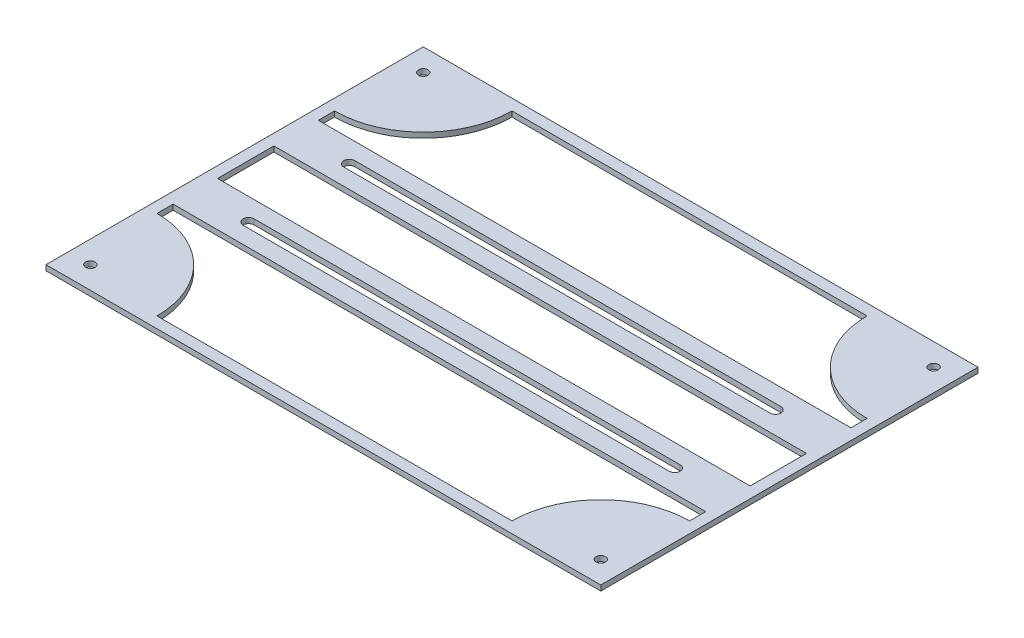
SolidWorks part; units mm, degrees
material "Acrylic (Medium-high impact)"
ref_plane "Front Plane" through (0, 0, 0) normal (0, 0, 1) x (1, 0, 0)
ref_plane "Top Plane" through (0, 0, 0) normal (0, 1, 0) x (1, 0, 0)
ref_plane "Right Plane" through (0, 0, 0) normal (1, 0, 0) x (0, 0, -1)
sketch "Sketch1" plane through (0, 0, 0) normal (0, 1, 0) x (1, 0, 0)
  line L0 (-76.2, -25.4) -> (-76.2, -20.7675)
  line L1 (79.375, -53.975) -> (-79.375, -53.975)
  line L2 (79.375, -53.975) -> (79.375, 53.975)
  line L3 (79.375, 53.975) -> (-79.375, 53.975)
  line L4 (-79.375, -53.975) -> (-79.375, 53.975)
  line L5 (79.375, -53.975) -> (-79.375, 53.975) construction
  line L6 (79.375, 53.975) -> (-79.375, -53.975) construction
  line L7 (50.8, -50.8) -> (-50.8, -50.8)
  line L8 (76.2, -25.4) -> (76.2, -20.7675)
  line L10 (76.2, -20.7675) -> (-76.2, -20.7675)
  line L11 (76.2, -8.0675) -> (-76.2, -8.0675)
  line L12 (0, 0) -> (-76.2, 0) construction
  line L13 (76.2, 8.0675) -> (-76.2, 8.0675)
  line L14 (76.2, 20.7675) -> (-76.2, 20.7675)
  line L15 (-76.2, -8.0675) -> (-76.2, 8.0675)
  line L16 (-76.2, -50.8) -> (-76.2, 50.8) construction
  line L17 (76.2, -8.0675) -> (76.2, 8.0675)
  line L18 (76.2, -50.8) -> (76.2, 50.8) construction
  line L19 (-76.2, 20.7675) -> (-76.2, 25.4)
  line L20 (76.2, 20.7675) -> (76.2, 25.4)
  line L21 (0, 0) -> (0, 34.6317) construction
  line L22 (76.2, 50.8) -> (-76.2, 50.8) construction
  line L23 (76.2, -50.8) -> (-76.2, -50.8) construction
  line L24 (50.8, 50.8) -> (-50.8, 50.8)
  arc A0 (-50.8, -50.8) -> (-76.2, -25.4) centre (-76.2, -50.8) ccw
  arc A1 (50.8, -50.8) -> (76.2, -25.4) centre (76.2, -50.8) cw
  arc A2 (50.8, 50.8) -> (76.2, 25.4) centre (76.2, 50.8) ccw
  arc A3 (-50.8, 50.8) -> (-76.2, 25.4) centre (-76.2, 50.8) cw
  point P0 (0, 0)
  dimension "D6" = 3.175
  dimension "D4" = 25.4
  dimension "D1" = 107.95
  dimension "D2" = 158.75
  dimension "D5" = 12.7
  dimension "D3" = 3.175
extrude "Boss-Extrude1" add sketch "Sketch1" along normal blind 1.524
sketch "Sketch3" plane through (0, 1.524, 0) normal (0, 1, 0) x (1, 0, 0)
  line L0 (-60.96, 14.4175) -> (60.96, 14.4175) construction
  line L1 (-60.96, 16.005) -> (60.96, 16.005)
  line L2 (-60.96, 12.83) -> (60.96, 12.83)
  line L3 (76.2, 20.7675) -> (-76.2, 20.7675) construction
  line L6 (76.2, 8.0675) -> (-76.2, 8.0675) construction
  line L7 (0, 0) -> (40.1052, 0) construction
  line L8 (-60.96, -14.4175) -> (60.96, -14.4175) construction
  line L9 (-60.96, -16.005) -> (60.96, -16.005)
  line L10 (-60.96, -12.83) -> (60.96, -12.83)
  arc A0 (-60.96, 16.005) -> (-60.96, 12.83) centre (-60.96, 14.4175) ccw
  arc A1 (60.96, 12.83) -> (60.96, 16.005) centre (60.96, 14.4175) ccw
  arc A2 (-60.96, -16.005) -> (-60.96, -12.83) centre (-60.96, -14.4175) cw
  arc A3 (60.96, -12.83) -> (60.96, -16.005) centre (60.96, -14.4175) cw
  point P2 (0, 14.4175)
  point P11 (0, 8.0675)
  point P17 (0, -14.4175)
  dimension "D1" = 1.5875
  dimension "D2" = 6.35
  dimension "D3" = 121.92
extrude "Cut-Extrude1" cut sketch "Sketch3" against normal through all
hole_wizard "#6-32 Tapped Hole1" positions "Sketch4" profile "Sketch5" tap size "#6-32" standard "Ansi Inch" end condition through all
sketch "Sketch4" plane through (0, 7.8105, 0) normal (0, 1, 0) x (-1, 0, 0)
  line L2 (0, 0) -> (0, 35.5851) construction
  line L4 (0, 0) -> (43.0458, 0) construction
  point P0 (73.025, -47.625)
  point P15 (73.025, 47.625)
  point P16 (-73.025, 47.625)
  point P17 (-73.025, -47.625)
sketch "Sketch5" plane through (-73.025, 7.8105, -47.625) normal (1, 0, 0) x (0, 0, 1)
  line L0 (0, 0) -> (0, 7.8105)
  line L1 (0, 7.8105) -> (1.3525, 7.8105)
  line L2 (1.3525, 7.8105) -> (1.3525, 0)
  line L3 (1.3525, 0) -> (0, 0)
  line L4 (0, -6.35) -> (0, 107.95) construction
  dimension "Thru Tap Drill Dia." = 2.7051
  dimension "Thru Tap Drill Depth" = 7.8105
cosmetic thread "Hole Thread1"
cosmetic thread "Hole Thread2"
cosmetic thread "Hole Thread3"
cosmetic thread "Hole Thread4"
hole_wizard "#6-32 Tapped Hole2" positions "Sketch6" profile "Sketch7" tap size "#6-32" standard "Ansi Inch" end condition through all
sketch "Sketch6" plane through (0, 1.524, 0) normal (0, 1, 0) x (-1, 0, 0)
  line L2 (0, 0) -> (0, 35.5851) construction
  line L4 (0, 0) -> (43.0458, 0) construction
  point P0 (73.025, -47.625)
  point P15 (73.025, 47.625)
  point P16 (-73.025, 47.625)
  point P17 (-73.025, -47.625)
sketch "Sketch7" plane through (-73.025, 1.524, -47.625) normal (1, 0, 0) x (0, 0, 1)
  line L0 (0, 0) -> (0, 1.524)
  line L1 (0, 1.524) -> (1.3525, 1.524)
  line L2 (1.3525, 1.524) -> (1.3525, 0)
  line L3 (1.3525, 0) -> (0, 0)
  line L4 (0, -6.35) -> (0, 107.95) construction
  dimension "Thru Tap Drill Dia." = 2.7051
  dimension "Thru Tap Drill Depth" = 1.524
equation "\"D2@Sketch3\" = \"D5@Sketch1\"/2"
